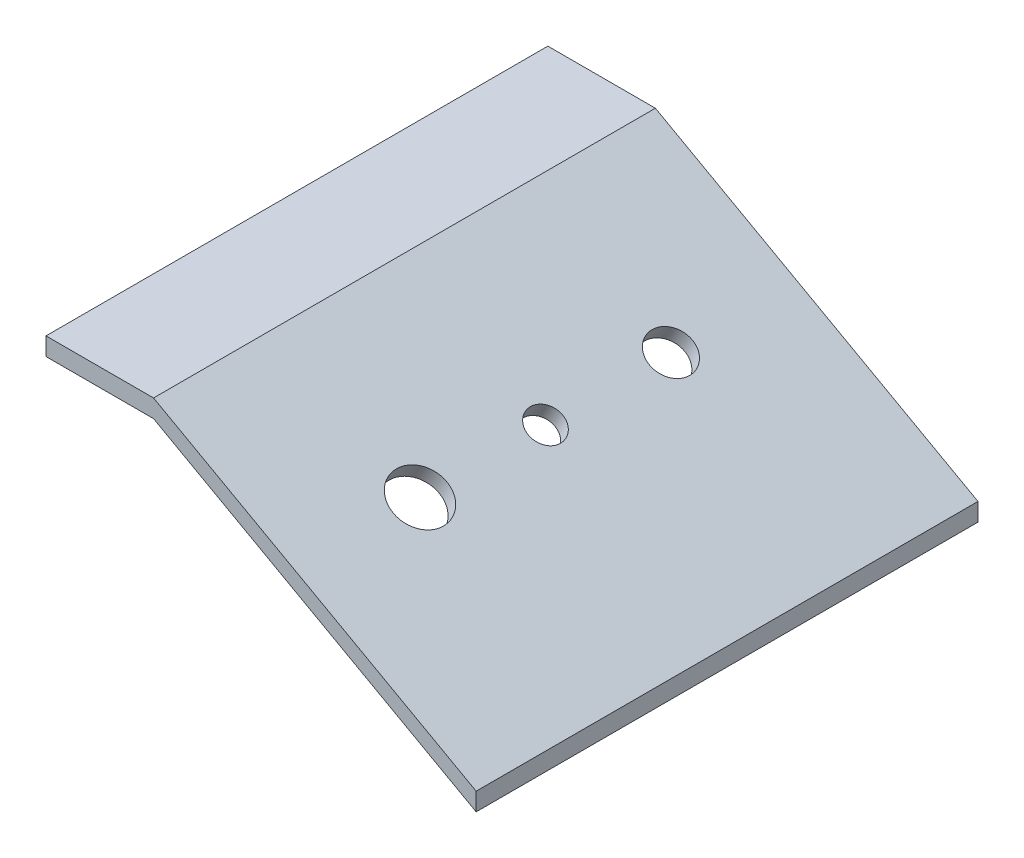
SolidWorks part; units mm, degrees
ref_plane "Front Plane" through (0, 0, 0) normal (0, 0, 1) x (1, 0, 0)
ref_plane "Top Plane" through (0, 0, 0) normal (0, 1, 0) x (1, 0, 0)
ref_plane "Right Plane" through (0, 0, 0) normal (1, 0, 0) x (0, 0, -1)
sketch "Sketch1" plane through (0, 0, 0) normal (0, 0, 1) x (1, 0, 0)
  line L0 (0, 0) -> (38.1, 0)
  line L3 (38.1, 0) -> (152.4, -63.5)
  line L4 (0, 0) -> (0, 6.35)
  line L6 (152.4, -63.5) -> (152.4, -57.15)
  line L7 (152.4, -57.15) -> (38.1, 6.35)
  line L8 (0, 6.35) -> (38.1, 6.35)
  dimension "D1" = 38.1
  dimension "D2" = 6.35
  dimension "D3" = 6.35
extrude "Boss-Extrude1" add sketch "Sketch1" along normal blind 152.4
sketch "Sketch2" plane through (11.6816, 21.0269, 0) normal (0.4856, 0.8742, 0) x (0.8742, -0.4856, 0)
  line L0 (160.9761, -152.4) -> (30.2216, -152.4) construction
  line L1 (160.9761, 0) -> (30.2216, 0) construction
  line L2 (30.2216, -152.4) -> (30.2216, 0) construction
  circle A0 centre (87.3716, -120.65) radius 9.525
  circle A1 centre (87.3716, -76.2) radius 6.096
  circle A2 centre (87.3716, -31.75) radius 7.62
  dimension "D1" = 19.05
  dimension "D2" = 15.24
  dimension "D3" = 12.192
  dimension "D4" = 31.75
  dimension "D5" = 31.75
  dimension "D6" = 44.45
  dimension "D7" = 57.15
  dimension "D8" = 57.15
  dimension "D9" = 57.15
extrude "Cut-Extrude1" cut sketch "Sketch2" against normal blind 152.4
sketch "Sketch3" plane through (0, 0, 0) normal (0, -1, 0) x (1, 0, 0)
  line L0 (0, 0) -> (38.1, 0) construction
  line L1 (0, 152.4) -> (0, 0) construction
  line L2 (0, 152.4) -> (38.1, 152.4) construction
  circle A0 centre (12.7, 6.35) radius 3.175
  circle A1 centre (12.7, 146.05) radius 3.175
  dimension "D1" = 6.35
  dimension "D2" = 6.35
  dimension "D3" = 6.35
  dimension "D4" = 12.7
  dimension "D5" = 12.7
  dimension "D6" = 6.35
extrude "Boss-Extrude2" add sketch "Sketch3" along normal blind 12.7
sketch "Sketch4" plane through (8.9858, 16.1745, 0) normal (-0.4856, -0.8742, 0) x (0.8742, -0.4856, 0)
  line L0 (33.3054, 0) -> (164.0599, 0) construction
  line L1 (164.0599, 152.4) -> (164.0599, 0) construction
  line L2 (33.3054, 152.4) -> (164.0599, 152.4) construction
  circle A0 centre (151.3599, 6.35) radius 3.175
  circle A1 centre (151.3599, 146.05) radius 3.175
  dimension "D1" = 6.35
  dimension "D2" = 6.35
  dimension "D3" = 6.35
  dimension "D4" = 12.7
  dimension "D5" = 6.35
  dimension "D6" = 12.7
extrude "Boss-Extrude3" add sketch "Sketch4" along normal blind 12.7
sketch "Sketch7" plane through (0, 0, 152.4) normal (0, 0, 1) x (1, 0, 0)
  line L0 (0, 0) -> (0, 6.35)
  line L1 (0, 6.35) -> (38.1, 6.35)
  line L2 (38.1, 6.35) -> (152.4, -57.15)
  line L3 (152.4, -57.15) -> (152.4, -63.5)
  line L4 (152.4, -63.5) -> (38.1, 0)
  line L5 (38.1, 0) -> (0, 0)
extrude "Boss-Extrude5" add sketch "Sketch7" along normal blind 12.7
sketch "Sketch8" plane through (0, 0, 0) normal (0, 0, -1) x (-1, 0, 0)
  line L0 (0, 0) -> (-38.1, 0)
  line L1 (-38.1, 0) -> (-152.4, -63.5)
  line L2 (-152.4, -63.5) -> (-152.4, -57.15)
  line L3 (-152.4, -57.15) -> (-38.1, 6.35)
  line L4 (-38.1, 6.35) -> (0, 6.35)
  line L5 (0, 6.35) -> (0, 0)
extrude "Boss-Extrude6" add sketch "Sketch8" along normal blind 12.7
